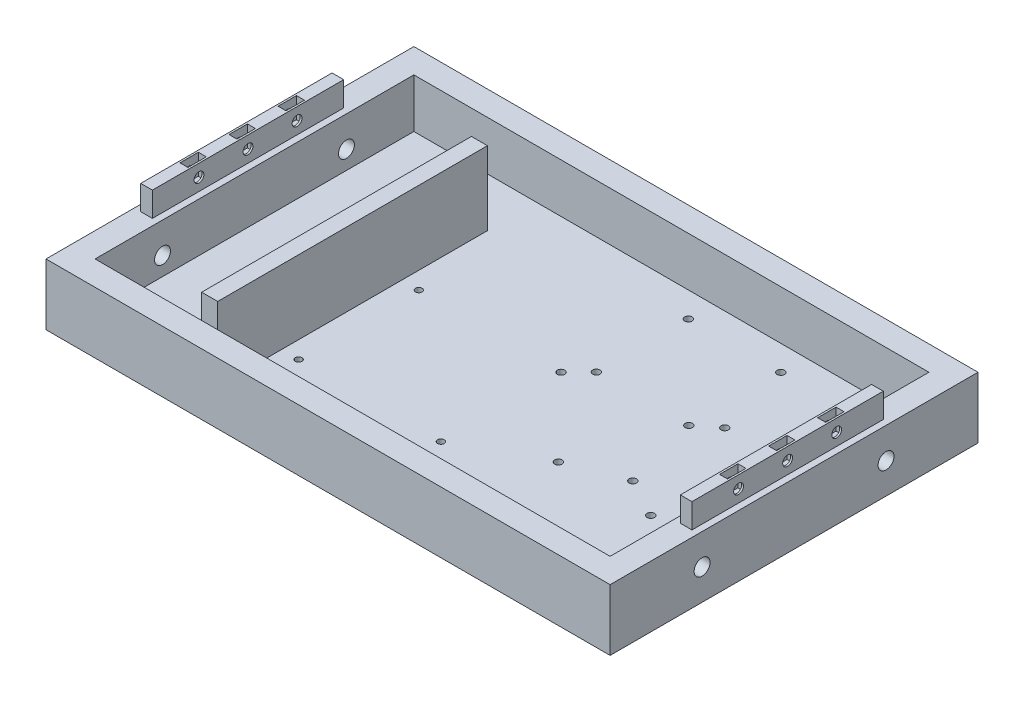
SolidWorks part; units mm, degrees
ref_plane "Front Plane" through (0, 0, 0) normal (0, 0, 1) x (1, 0, 0)
ref_plane "Top Plane" through (0, 0, 0) normal (0, 1, 0) x (1, 0, 0)
ref_plane "Right Plane" through (0, 0, 0) normal (1, 0, 0) x (0, 0, -1)
sketch "Sketch1" plane through (0, 0, 0) normal (0, 0, 1) x (1, 0, 0)
  line L1 (0, 0) -> (230, 0)
  line L2 (0, 0) -> (0, 25)
  line L3 (0, 25) -> (230, 25)
  line L4 (230, 0) -> (230, 25)
  dimension "D1" = 25
  dimension "D2" = 230
extrude "Boss-Extrude1" add sketch "Sketch1" along normal blind 150
sketch "Sketch2" plane through (0, 25, 0) normal (0, 1, 0) x (1, 0, 0)
  line L0 (0, -150) -> (0, 0) construction
  line L1 (10, -10) -> (220, -10)
  line L2 (10, -10) -> (10, -140)
  line L3 (10, -140) -> (220, -140)
  line L4 (220, -10) -> (220, -140)
  line L5 (230, 0) -> (0, 0) construction
  line L6 (230, -150) -> (230, 0) construction
  line L7 (230, -150) -> (0, -150) construction
  dimension "D1" = 10
  dimension "D2" = 10
  dimension "D3" = 10
  dimension "D4" = 10
extrude "Cut-Extrude1" cut sketch "Sketch2" against normal blind 20
sketch "Sketch4" plane through (0, 5, 0) normal (0, 1, 0) x (1, 0, 0)
  line L0 (10, -140) -> (220, -140) construction
  line L1 (53.472, -140) -> (60, -140)
  line L2 (53.472, -140) -> (53.472, -30)
  line L3 (53.472, -30) -> (60, -30)
  line L4 (60, -140) -> (60, -30)
  line L5 (10, -10) -> (10, -140) construction
  dimension "D1" = 50
  dimension "D2" = 110
extrude "Boss-Extrude3" add sketch "Sketch4" along normal blind 30
sketch "Sketch5" plane through (0, 5, 0) normal (0, 1, 0) x (1, 0, 0)
  line L0 (67, 0) -> (67, -65) construction
  line L1 (230, 0) -> (0, 0) construction
  line L2 (67, -65) -> (10, -65) construction
  line L3 (10, -10) -> (10, -140) construction
  line L4 (67, -65) -> (67, -114) construction
  line L5 (67, -65) -> (125, -65) construction
  line L6 (67, -114) -> (125, -114) construction
  circle A0 centre (67, -65) radius 1.35
  circle A1 centre (67, -114) radius 1.35
  circle A2 centre (125, -65) radius 1.5
  circle A3 centre (125, -114) radius 1.35
  dimension "D2" = 58
  dimension "D3" = 58
  dimension "D4" = 3
  dimension "D1" = 57
  dimension "D5" = 65
  dimension "D6" = 49
extrude "Cut-Extrude2" cut sketch "Sketch5" against normal up to next
sketch "Sketch6" plane through (0, 5, 0) normal (0, 1, 0) x (1, 0, 0)
  line L0 (0, 0) -> (0, -39) construction
  line L1 (0, -150) -> (0, 0) construction
  line L2 (0, -39) -> (151, -39) construction
  line L3 (0, 0) -> (0, -70) construction
  line L4 (0, -70) -> (196.85, -70) construction
  line L5 (0, 0) -> (0, -116) construction
  line L6 (0, -116) -> (175, -116) construction
  line L7 (151, -39) -> (151, -17.25) construction
  line L8 (151, -39) -> (129.15, -39) construction
  line L13 (196.85, -70) -> (175, -70) construction
  line L14 (196.85, -70) -> (196.85, -48.25) construction
  line L15 (175, -116) -> (153.15, -116) construction
  line L20 (175, -116) -> (175, -94.25) construction
  circle A0 centre (132.15, -20.25) radius 1.5
  circle A1 centre (169.85, -20.25) radius 1.5
  circle A2 centre (169.85, -57.75) radius 1.5
  circle A3 centre (132.15, -57.75) radius 1.5
  circle A4 centre (178, -51.25) radius 1.5
  circle A5 centre (215.7, -51.25) radius 1.5
  circle A6 centre (215.7, -88.75) radius 1.5
  circle A7 centre (178, -88.75) radius 1.5
  circle A8 centre (156.15, -97.25) radius 1.5
  circle A9 centre (193.85, -97.25) radius 1.5
  circle A10 centre (193.85, -134.75) radius 1.5
  circle A11 centre (156.15, -134.75) radius 1.5
  point P16 (172.85, -39)
  dimension "D1" = 37.5
  dimension "D2" = 37.7
  dimension "D3" = 21.85
  dimension "D5" = 3
  dimension "D6" = 3
  dimension "D7" = 37.5
  dimension "D8" = 3
  dimension "D4" = 21.75
extrude "Cut-Extrude3" cut sketch "Sketch6" against normal through all
sketch "Sketch7" plane through (0, 0, 0) normal (-1, 0, 0) x (0, 0, 1)
  line L0 (0, 12.5) -> (75, 12.5) construction
  line L1 (0, 25) -> (0, 0) construction
  line L3 (75, 12.5) -> (75, 25) construction
  line L4 (150, 25) -> (0, 25) construction
  circle A0 centre (37.5, 12.5) radius 3.25
  circle A1 centre (112.5, 12.5) radius 3.25
extrude "Cut-Extrude4" cut sketch "Sketch7" against normal up to next
sketch "Sketch8" plane through (220, 0, 0) normal (-1, 0, 0) x (0, 0, 1)
  circle A0 centre (112.5, 12.5) radius 3.25 construction
  circle A1 centre (37.5, 12.5) radius 3.25 construction
  circle A2 centre (112.5, 12.5) radius 3.25
  circle A3 centre (37.5, 12.5) radius 3.25
extrude "Cut-Extrude5" cut sketch "Sketch8" against normal up to next
sketch "Sketch9" plane through (0, 25, 0) normal (0, 1, 0) x (1, 0, 0)
  line L0 (115, 0) -> (115, -150) construction
  line L1 (230, 0) -> (0, 0) construction
  line L2 (230, -150) -> (0, -150) construction
  line L8 (5, -10) -> (5, -140) construction
  line L9 (0, -75) -> (10, -75) construction
  line L10 (7.375, -115) -> (2.625, -115)
  line L13 (7.375, -35) -> (2.625, -35)
  line L14 (2.625, -115) -> (2.625, -35)
  line L15 (7.375, -115) -> (7.375, -35)
  line L16 (222.625, -115) -> (227.375, -115)
  line L17 (222.625, -115) -> (222.625, -35)
  line L18 (227.375, -115) -> (227.375, -35)
  line L19 (222.625, -35) -> (227.375, -35)
  point P17 (2.625, -75)
  point P18 (5, -115)
  point P19 (5, -35)
extrude "Boss-Extrude4" add sketch "Sketch9" along normal blind 10
sketch "Sketch10" plane through (2.625, 0, 0) normal (-1, 0, 0) x (0, 0, 1)
  line L0 (35, 30) -> (75, 30) construction
  line L1 (35, 35) -> (35, 25) construction
  line L3 (75, 30) -> (75, 35) construction
  line L4 (35, 35) -> (115, 35) construction
  circle A0 centre (55, 30) radius 2
  circle A1 centre (75, 30) radius 2
  circle A2 centre (95, 30) radius 2
extrude "Cut-Extrude6" cut sketch "Sketch10" against normal blind 10
sketch "Sketch11" plane through (222.625, 0, 0) normal (-1, 0, 0) x (0, 0, 1)
  circle A0 centre (95, 30) radius 2 construction
  circle A1 centre (75, 30) radius 2 construction
  circle A2 centre (55, 30) radius 2 construction
  circle A3 centre (95, 30) radius 2
  circle A4 centre (75, 30) radius 2
  circle A5 centre (55, 30) radius 2
extrude "Cut-Extrude7" cut sketch "Sketch11" against normal blind 10
sketch "Sketch12" plane through (0, 35, 0) normal (0, 1, 0) x (1, 0, 0)
  line L0 (5, -35) -> (5, -115) construction
  line L1 (7.375, -35) -> (2.625, -35) construction
  line L2 (2.625, -115) -> (7.375, -115) construction
  line L3 (5, -75) -> (2.625, -75) construction
  line L4 (2.625, -35) -> (2.625, -115) construction
  line L5 (115, 0) -> (115, -150) construction
  line L6 (230, 0) -> (0, 0) construction
  line L7 (230, -150) -> (0, -150) construction
  line L8 (6.625, -78.75) -> (3.375, -78.75)
  line L11 (6.625, -71.25) -> (3.375, -71.25)
  line L12 (3.375, -78.75) -> (3.375, -71.25)
  line L13 (6.625, -78.75) -> (6.625, -71.25)
  line L14 (5, -75) -> (5, -95) construction
  line L15 (5, -85) -> (0, -85) construction
  line L16 (0, -150) -> (0, 0) construction
  line L17 (6.625, -91.25) -> (3.375, -91.25)
  line L18 (6.625, -91.25) -> (6.625, -98.75)
  line L19 (6.625, -98.75) -> (3.375, -98.75)
  line L20 (3.375, -91.25) -> (3.375, -98.75)
  line L21 (6.625, -51.25) -> (3.375, -51.25)
  line L22 (6.625, -58.75) -> (6.625, -51.25)
  line L23 (3.375, -58.75) -> (3.375, -51.25)
  line L24 (6.625, -58.75) -> (3.375, -58.75)
  line L25 (223.375, -91.25) -> (226.625, -91.25)
  line L26 (226.625, -91.25) -> (226.625, -98.75)
  line L27 (223.375, -98.75) -> (226.625, -98.75)
  line L28 (223.375, -91.25) -> (223.375, -98.75)
  line L29 (223.375, -78.75) -> (226.625, -78.75)
  line L30 (226.625, -78.75) -> (226.625, -71.25)
  line L31 (223.375, -78.75) -> (223.375, -71.25)
  line L32 (223.375, -71.25) -> (226.625, -71.25)
  line L33 (223.375, -58.75) -> (226.625, -58.75)
  line L34 (223.375, -58.75) -> (223.375, -51.25)
  line L35 (223.375, -51.25) -> (226.625, -51.25)
  line L36 (226.625, -58.75) -> (226.625, -51.25)
  point P20 (3.375, -75)
  point P22 (5, -78.75)
  point P23 (5, -71.25)
  dimension "D1" = 1.625
extrude "Cut-Extrude8" cut sketch "Sketch12" against normal blind 8.5
sketch "Sketch13" plane through (0, 35, 0) normal (0, 1, 0) x (1, 0, 0)
  line L0 (227.375, -115) -> (227.375, -35) construction
  line L1 (222.625, -35) -> (227.375, -35)
  line L2 (222.625, -35) -> (222.625, -36)
  line L3 (222.625, -36) -> (227.375, -36)
  line L4 (227.375, -35) -> (227.375, -36)
  line L5 (115, 0) -> (115, -150) construction
  line L6 (222.625, -115) -> (227.375, -115)
  line L7 (222.625, -115) -> (222.625, -114)
  line L8 (222.625, -114) -> (227.375, -114)
  line L9 (227.375, -115) -> (227.375, -114)
  line L10 (230, 0) -> (0, 0) construction
  line L11 (230, -150) -> (0, -150) construction
  line L12 (7.375, -36) -> (2.625, -36)
  line L13 (2.625, -35) -> (2.625, -36)
  line L14 (7.375, -35) -> (2.625, -35)
  line L15 (7.375, -35) -> (7.375, -36)
  line L16 (7.375, -114) -> (2.625, -114)
  line L17 (2.625, -115) -> (2.625, -114)
  line L18 (7.375, -115) -> (2.625, -115)
  line L19 (7.375, -115) -> (7.375, -114)
  dimension "D1" = 1
  dimension "D2" = 1
extrude "Cut-Extrude9" cut sketch "Sketch13" against normal blind 10
